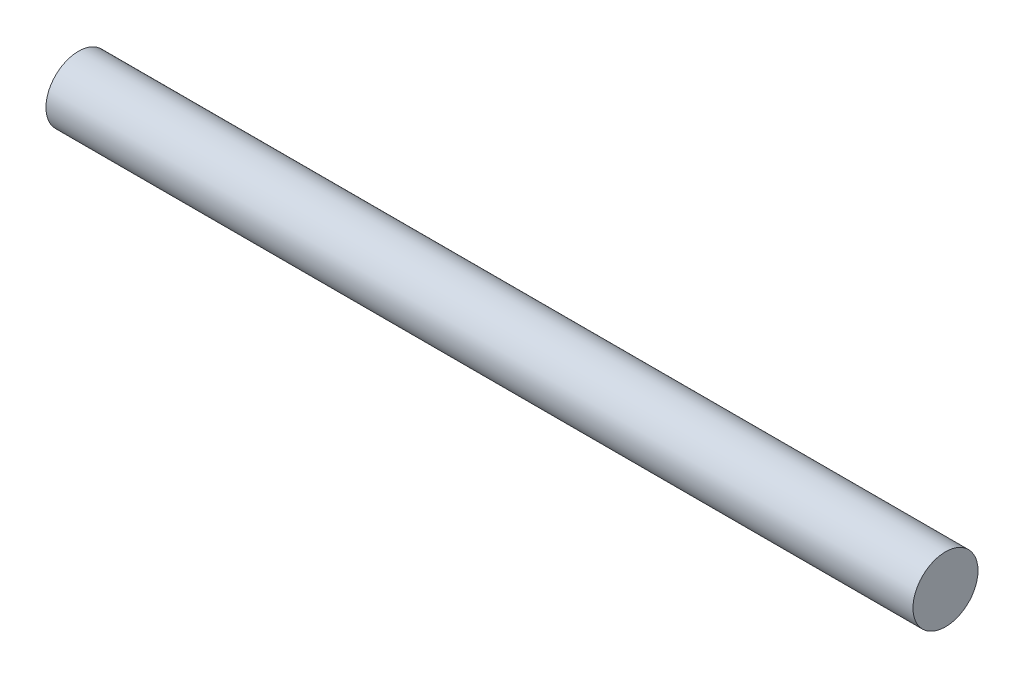
SolidWorks part; units mm, degrees
ref_plane "Front Plane" through (0, 0, 0) normal (0, 0, 1) x (1, 0, 0)
ref_plane "Top Plane" through (0, 0, 0) normal (0, 1, 0) x (1, 0, 0)
ref_plane "Right Plane" through (0, 0, 0) normal (1, 0, 0) x (0, 0, -1)
sketch "Sketch1" plane through (0, 0, 0) normal (1, 0, 0) x (0, 0, -1)
  circle A0 centre (-22.6945, 11.063) radius 0.75
  dimension "D1" = 1.5
extrude "Boss-Extrude1" add sketch "Sketch1" along normal blind 20
